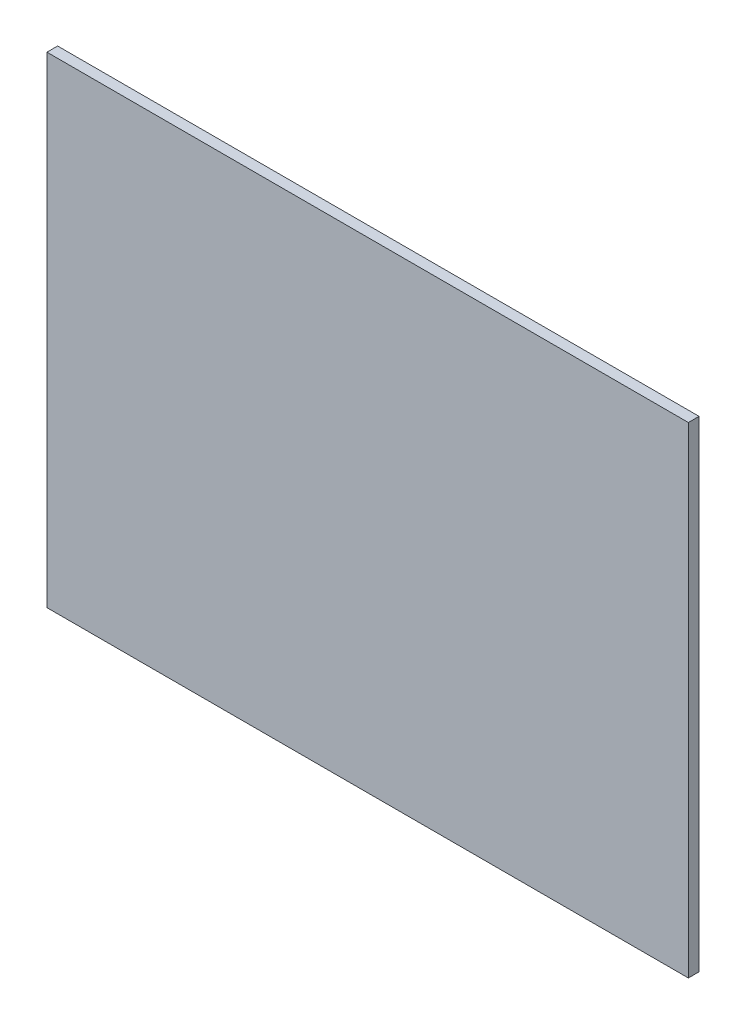
SolidWorks part; units mm, degrees
ref_plane "Front Plane" through (0, 0, 0) normal (0, 0, 1) x (1, 0, 0)
ref_plane "Top Plane" through (0, 0, 0) normal (0, 1, 0) x (1, 0, 0)
ref_plane "Right Plane" through (0, 0, 0) normal (1, 0, 0) x (0, 0, -1)
sketch "Sketch1" plane through (0, 0, 0) normal (0, 0, 1) x (1, 0, 0)
  line L1 (-25.8167, 24.2032) -> (34.1833, 24.2032)
  line L2 (-25.8167, 24.2032) -> (-25.8167, -20.7968)
  line L3 (-25.8167, -20.7968) -> (34.1833, -20.7968)
  line L4 (34.1833, 24.2032) -> (34.1833, -20.7968)
  dimension "D1" = 60
  dimension "D2" = 45
extrude "Boss-Extrude1" add sketch "Sketch1" along normal blind 1
sketch "Sketch2" plane through (0, 0, 0) normal (0, 0, -1) x (-1, 0, 0)
  line L0 (-25.5848, 18.2878) -> (14.9553, 18.6757) construction
  text T0 "SL\r\n"
